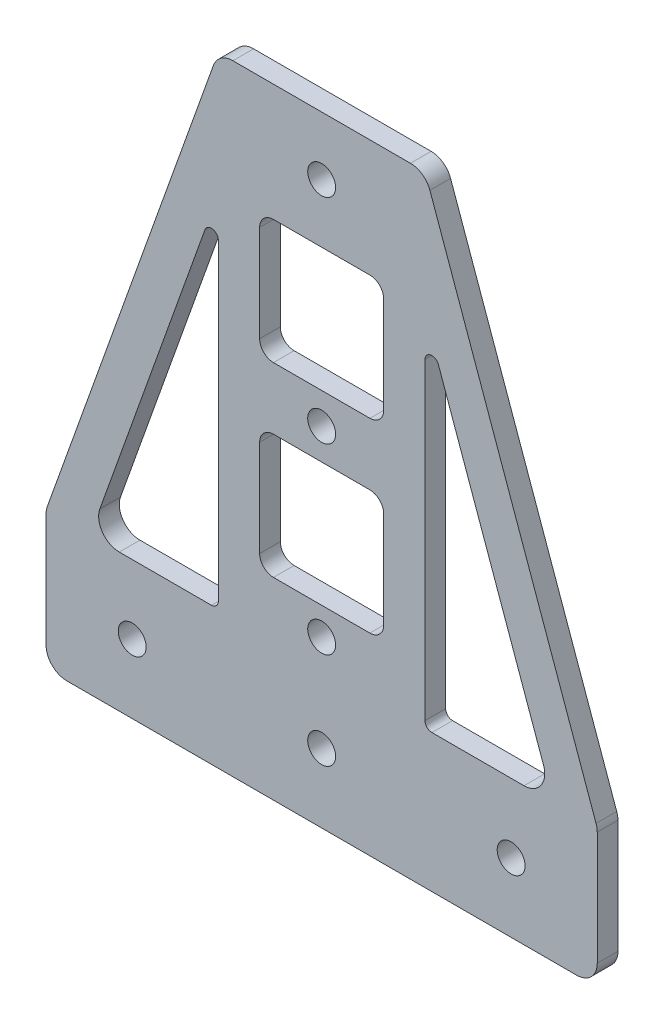
SolidWorks part; units mm, degrees
material "Thornel Mat VMA"
ref_plane "前视基准面" through (0, 0, 0) normal (0, 0, 1) x (1, 0, 0)
ref_plane "上视基准面" through (0, 0, 0) normal (0, 1, 0) x (1, 0, 0)
ref_plane "右视基准面" through (0, 0, 0) normal (1, 0, 0) x (0, 0, -1)
other "Configuration Table"
sketch "草图1" plane through (0, 0, 0) normal (0, 0, 1) x (1, 0, 0)
  line L8 (40, 0) -> (-40, 0)
  line L9 (-40, 0) -> (-40, 20)
  line L10 (-40, 20) -> (-15, 90)
  line L11 (-15, 90) -> (15, 90)
  line L12 (15, 90) -> (40, 20)
  line L13 (40, 20) -> (40, 0)
  line L14 (0, 0) -> (0, 90) construction
  dimension "D1" = 20
  dimension "D2" = 30
  dimension "D3" = 90
  dimension "D4" = 80
extrude "凸台-拉伸1" add sketch "草图1" along normal mid plane 3
sketch "草图2" plane through (0, 0, 1.5) normal (0, 0, 1) x (1, 0, 0)
  line L0 (-15, 72.1607) -> (-33.6288, 20)
  line L3 (-33.6288, 20) -> (-15, 20)
  line L10 (-15, 20) -> (-15, 72.1607)
  line L11 (-15, 90) -> (-40, 20) construction
  line L12 (-40, 0) -> (40, 0) construction
  line L13 (-40, 20) -> (-40, 0) construction
  line L14 (0, 0) -> (0, 28) construction
  line L15 (-9, 55) -> (9, 55)
  line L16 (-9, 55) -> (-9, 73)
  line L17 (-9, 73) -> (9, 73)
  line L18 (9, 55) -> (9, 73)
  line L19 (-9, 55) -> (9, 73) construction
  line L20 (-9, 73) -> (9, 55) construction
  line L21 (-9, 28) -> (9, 28)
  line L22 (-9, 28) -> (-9, 46)
  line L23 (-9, 46) -> (9, 46)
  line L24 (9, 28) -> (9, 46)
  line L25 (-9, 28) -> (9, 46) construction
  line L26 (-9, 46) -> (9, 28) construction
  line L27 (15, 20) -> (15, 72.1607)
  line L28 (33.6288, 20) -> (15, 20)
  line L29 (15, 72.1607) -> (33.6288, 20)
  point P2 (0, 37)
  point P11 (0, 64)
  dimension "D1" = 6
  dimension "D5" = 28
  dimension "D2" = 20
  dimension "D3" = 25
  dimension "D4" = 18
  dimension "D6" = 9
extrude "切除-拉伸1" cut sketch "草图2" against normal up to surface (3 mm away) up to face at (0, 36.6667, -1.5)
fillet "圆角1" radius 1 4 edges at (15, 20, 0) (15, 72.1607, 0) (-15, 20, 0) (-15, 72.1607, 0)
fillet "圆角2" radius 2 8 edges at (9, 73, 0) (9, 55, 0) (-9, 55, 0) (-9, 73, 0) (9, 28, 0) (-9, 46, 0) (9, 46, 0) (-9, 28, 0)
fillet "圆角3" radius 3 6 edges at (40, 0, 0) (-40, 0, 0) (-40, 20, 0) (15, 90, 0) (40, 20, 0) (-15, 90, 0)
sketch "草图3" plane through (0, 0, 1.5) normal (0, 0, 1) x (1, 0, 0)
  line L0 (-37, 0) -> (37, 0) construction
  line L1 (0, 0) -> (0, 28) construction
  line L2 (-7, 28) -> (7, 28) construction
  circle A0 centre (-27.5, 10) radius 2.025
  circle A1 centre (27.5, 10) radius 2.025
  dimension "D1" = 55
  dimension "D2" = 4.05
  dimension "D3" = 10
extrude "切除-拉伸2" cut sketch "草图3" against normal through all both and the other way through all
sketch "草图4" plane through (0, 0, 1.5) normal (0, 0, 1) x (1, 0, 0)
  line L0 (-27.5, 10) -> (0, 10) construction
  circle A0 centre (0, 10) radius 2.025
  dimension "D1" = 4.05
extrude "切除-拉伸3" cut sketch "草图4" against normal through all both
sketch "草图5" plane through (0, 0, 1.5) normal (0, 0, 1) x (1, 0, 0)
  line L0 (-7, 28) -> (7, 28) construction
  line L1 (0, 55) -> (0, 46) construction
  line L2 (-7, 55) -> (7, 55) construction
  line L3 (7, 46) -> (-7, 46) construction
  line L4 (0, 73) -> (0, 90) construction
  line L5 (7, 73) -> (-7, 73) construction
  line L6 (12.8858, 90) -> (-12.8858, 90) construction
  circle A0 centre (0, 24) radius 2.025
  circle A1 centre (0, 50.5) radius 2.025
  circle A2 centre (0, 81.5) radius 2.025
  dimension "D1" = 4.05
  dimension "D2" = 4
extrude "切除-拉伸4" cut sketch "草图5" against normal through all both
fillet "圆角4" radius 3 2 edges at (33.6288, 20, 0) (-33.6288, 20, 0)
